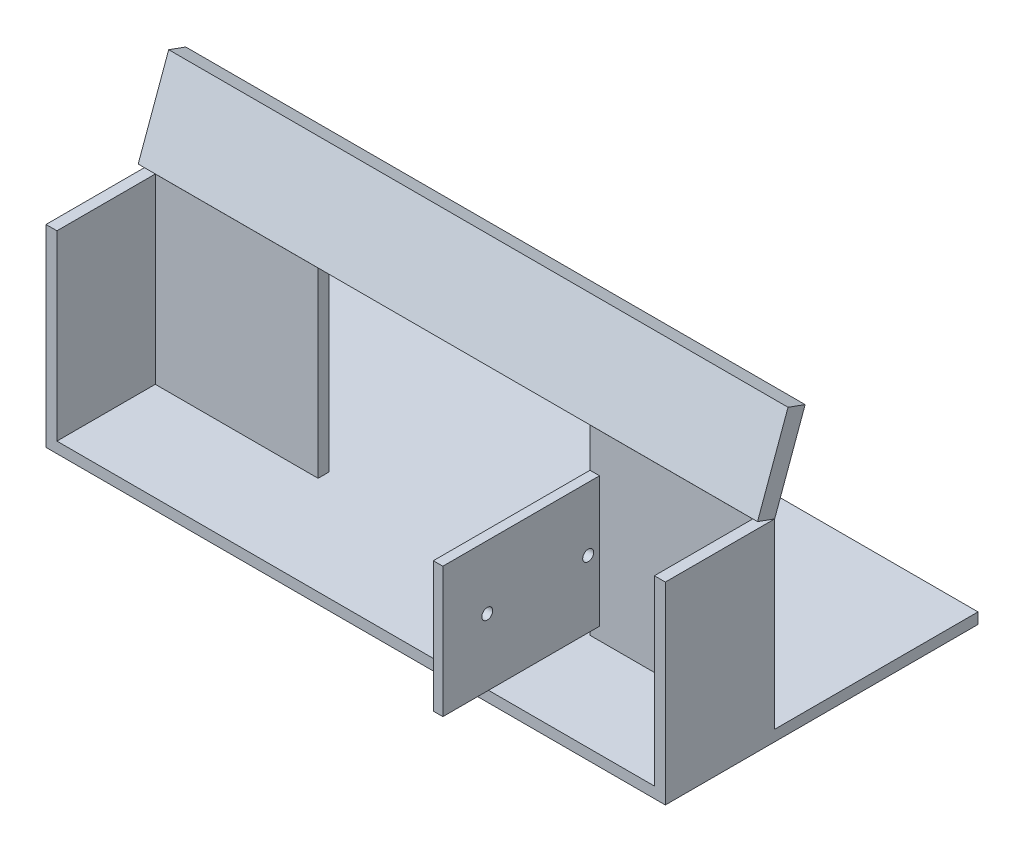
SolidWorks part; units mm, degrees
ref_plane "前视基准面" through (0, 0, 0) normal (0, 0, 1) x (1, 0, 0)
ref_plane "上视基准面" through (0, 0, 0) normal (0, 1, 0) x (1, 0, 0)
ref_plane "右视基准面" through (0, 0, 0) normal (1, 0, 0) x (0, 0, -1)
sketch "草图1" plane through (0, 0, 0) normal (0, 1, 0) x (1, 0, 0)
  line L1 (-85, -15) -> (85, -15)
  line L2 (-85, -15) -> (-85, 15)
  line L3 (-85, 15) -> (85, 15)
  line L4 (85, -15) -> (85, 15)
  line L5 (-85, -15) -> (85, 15) construction
  line L6 (-85, 15) -> (85, -15) construction
  line L7 (-82, -12) -> (82, -12)
  line L8 (-82, -12) -> (-82, 12)
  line L9 (-82, 12) -> (82, 12)
  line L10 (82, -12) -> (82, 12)
  line L11 (-82, -12) -> (82, 12) construction
  line L12 (-82, 12) -> (82, -12) construction
  point P0 (0, 0)
  point P6 (0, 0)
  dimension "D1" = 3
  dimension "D2" = 3
  dimension "D3" = 170
  dimension "D4" = 30
extrude "凸台-拉伸1" add sketch "草图1" along normal blind 50
ref_plane "基准面1" through (0, 1.028, 2.8244) normal (0, 0.342, 0.9397) x (-1, 0, 0)
sketch "草图2" plane through (0, 1.028, 2.8244) normal (0, 0.342, 0.9397) x (-1, 0, 0)
  line L0 (85, -52.1149) -> (85, -41.8543) construction
  line L1 (-85, -52.1149) -> (85, -52.1149)
  line L2 (-85, -52.1149) -> (-85, -56.5908)
  line L3 (-85, -56.5908) -> (85, -56.5908)
  line L4 (85, -52.1149) -> (85, -56.5908)
  point P7 (-85, -62.9025)
  point P8 (-85, -56.5908)
extrude "凸台-拉伸2" add sketch "草图2" along normal blind 5
sketch "草图4" plane through (0, 53.178, -19.3552) normal (0, 0.9397, -0.342) x (1, 0, 0)
  line L0 (85, -8.0056) -> (85, -3.0056) construction
  line L1 (-85, -3.0056) -> (85, -3.0056)
  line L2 (-85, -3.0056) -> (-85, -8.0056)
  line L3 (-85, -8.0056) -> (85, -8.0056)
  line L4 (85, -3.0056) -> (85, -8.0056)
  line L5 (85, -8.0056) -> (-85, -8.0056) construction
  point P7 (85, -8.0056)
extrude "凸台-拉伸4" add sketch "草图4" along normal blind 20
sketch "草图5" plane through (0, 50, 0) normal (0, 1, 0) x (1, 0, 0)
  line L0 (-85, -15) -> (85, -15) construction
  line L1 (-82, -12) -> (82, -12)
  line L2 (-82, -12) -> (-82, -15)
  line L3 (-82, -15) -> (82, -15)
  line L4 (82, -12) -> (82, -15)
  line L5 (82, -12) -> (82, 12) construction
  point P5 (81.6779, -15)
extrude "切除-拉伸1" cut sketch "草图5" against normal through all
sketch "草图6" plane through (0, 0, 0) normal (0, -1, 0) x (1, 0, 0)
  line L0 (85, 15) -> (85, -15) construction
  line L1 (-85, 15) -> (85, 15)
  line L2 (-85, 15) -> (-85, -70.8174)
  line L3 (-85, -70.8174) -> (85, -70.8174)
  line L4 (85, 15) -> (85, -70.8174)
extrude "凸台-拉伸5" add sketch "草图6" along normal blind 3
sketch "草图7" plane through (0, 0, -12) normal (0, 0, 1) x (1, 0, 0)
  line L0 (82, 0) -> (-82, 0) construction
  line L1 (-37.3162, 0) -> (37.3162, 0)
  line L2 (-37.3162, 0) -> (-37.3162, 50)
  line L3 (-37.3162, 50) -> (37.3162, 50)
  line L4 (37.3162, 0) -> (37.3162, 50)
  line L5 (82, 50) -> (-82, 50) construction
  point P8 (0, 0)
extrude "切除-拉伸2" cut sketch "草图7" against normal through all
sketch "草图8" plane through (0, 0, -12) normal (0, 0, 1) x (1, 0, 0)
  line L0 (37.3162, 0) -> (37.3162, 50) construction
  line L1 (37.3162, 39.2303) -> (39.9315, 39.2303)
  line L2 (37.3162, 39.2303) -> (37.3162, 3.4613)
  line L3 (37.3162, 3.4613) -> (39.9315, 3.4613)
  line L4 (39.9315, 39.2303) -> (39.9315, 3.4613)
  point P6 (37.3162, 3.4613)
  point P7 (37.3162, 39.4107)
  point P8 (39.9315, 39.2303)
extrude "凸台-拉伸6" add sketch "草图8" along normal blind 43
sketch "草图10" plane through (39.9315, 0, 0) normal (1, 0, 0) x (0, 0, -1)
  line L0 (-18.8153, 21.8366) -> (8.8847, 21.8366) construction
  circle A0 centre (-18.8153, 21.8366) radius 1.5
  circle A1 centre (8.8847, 21.8366) radius 1.5
  point P4 (8.8847, 38.8583)
  dimension "D1" = 3
  dimension "D2" = 3
  dimension "D3" = 27.7
extrude "切除-拉伸3" cut sketch "草图10" against normal blind 13
